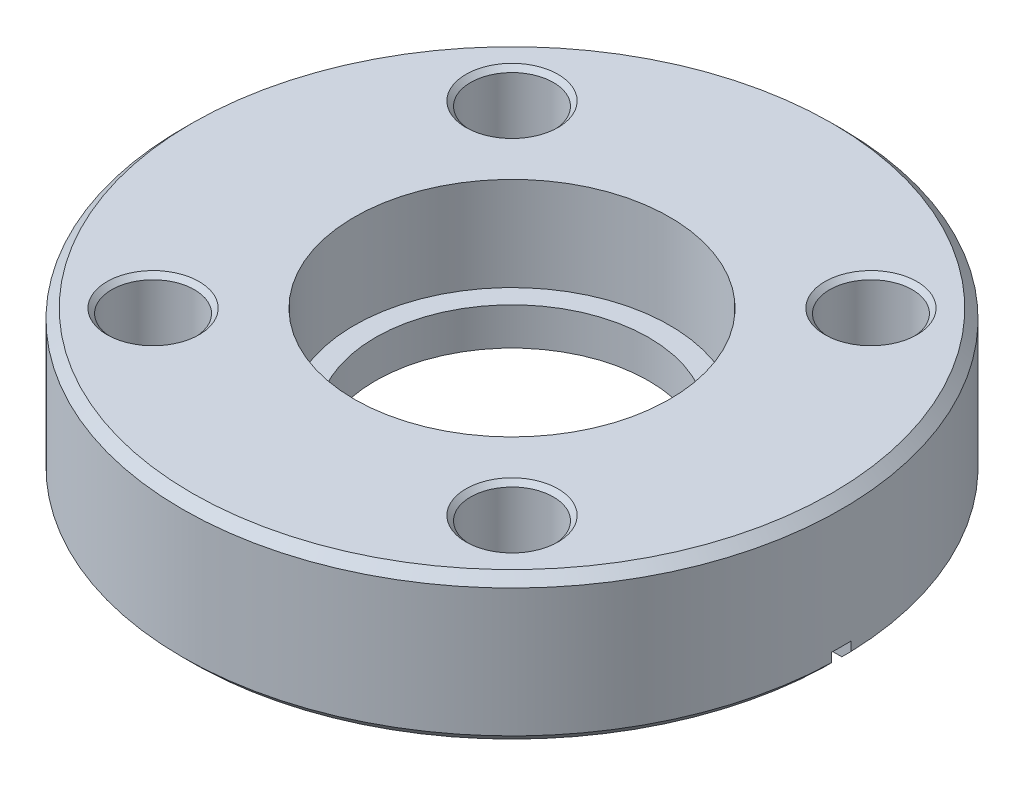
SolidWorks part; units mm, degrees
ref_plane "Front Plane" through (0, 0, 0) normal (0, 0, 1) x (1, 0, 0)
ref_plane "Top Plane" through (0, 0, 0) normal (0, 1, 0) x (1, 0, 0)
ref_plane "Right Plane" through (0, 0, 0) normal (1, 0, 0) x (0, 0, -1)
sketch "Sketch1" plane through (0, 0, 0) normal (0, 1, 0) x (1, 0, 0)
  circle A0 centre (0, 0) radius 26.797
  circle A1 centre (0, 0) radius 11.1125
  dimension "D1" = 53.594
  dimension "D2" = 22.225
extrude "Boss-Extrude1" add sketch "Sketch1" along normal blind 11.938
sketch "Sketch2" plane through (0, 11.938, 0) normal (0, 1, 0) x (1, 0, 0)
  circle A0 centre (0, 0) radius 12.827
  dimension "D1" = 25.654
extrude "Cut-Extrude1" cut sketch "Sketch2" against normal blind 7.62
chamfer "Chamfer1" distance 0.762 angle 45 2 edges at (0, 0, 26.797) (0, 11.938, 26.797)
sketch "Sketch3" plane through (0, 0, 0) normal (0, 0, 1) x (1, 0, 0)
  line L0 (-16.51, 0) -> (-16.51, 1.2446)
  line L1 (-16.51, 1.2446) -> (-13.843, 0.6604)
  line L2 (-13.843, 0.6604) -> (-13.843, 1.27)
  line L3 (-13.843, 1.27) -> (0, 1.27)
  line L4 (-16.51, 0) -> (0, 0)
  line L5 (0, 0) -> (0, 1.27)
  dimension "D1" = 16.51
  dimension "D2" = 13.843
  dimension "D3" = 1.2446
  dimension "D4" = 0.6096
  dimension "D5" = 1.27
revolve "Cut-Revolve1" cut sketch "Sketch3" angle 360 about axis through (0, 11.938, 0) along (0, -1, 0)
sketch "Sketch4" plane through (0, 0, 0) normal (0, 1, 0) x (1, 0, 0)
  line L0 (0, 0) -> (14.5929, 14.5929) construction
  line L1 (0, 0) -> (19.19, 0) construction
  circle A0 centre (14.5929, 14.5929) radius 3.3655
  dimension "D1" = 6.731
  dimension "D2" = 20.6375
  dimension "D4" = 45
extrude "Cut-Extrude2" cut sketch "Sketch4" along normal through all
chamfer "Chamfer2" distance 0.381 angle 45 2 edges at (14.5929, 11.938, -11.2274) (14.5929, 0, -11.2274)
pattern_circular "CirPattern1" count 4 every 90 about axis through (0, 0, 0) along (0, 1, 0) of "Cut-Extrude2", "Chamfer2"
sketch "Sketch5" plane through (0, 0, 0) normal (0, 0, 1) x (1, 0, 0)
  line L0 (0, 0) -> (0, 0.1) construction
  line L1 (-26.035, 0) -> (26.035, 0) construction
  line L2 (0, 0.1) -> (-15.875, 0.932) construction
  line L4 (-15.875, 0.932) -> (-28.575, 1.5976)
  line L5 (-15.875, 0) -> (0, 0) construction
  line L6 (-15.875, 0.932) -> (-15.875, 0)
  line L7 (-28.575, 1.5976) -> (-28.575, 0)
  line L8 (-28.575, 0) -> (-15.875, 0)
  dimension "D1" = 0.1
  dimension "D2" = 3
  dimension "D3" = 15.875
  dimension "D4" = 28.575
extrude "Cut-Extrude5" cut sketch "Sketch5" against normal mid plane 1.5875
mirror "Mirror1" about plane through (0, 0, 0) normal (1, 0, 0) of "Cut-Extrude5"
